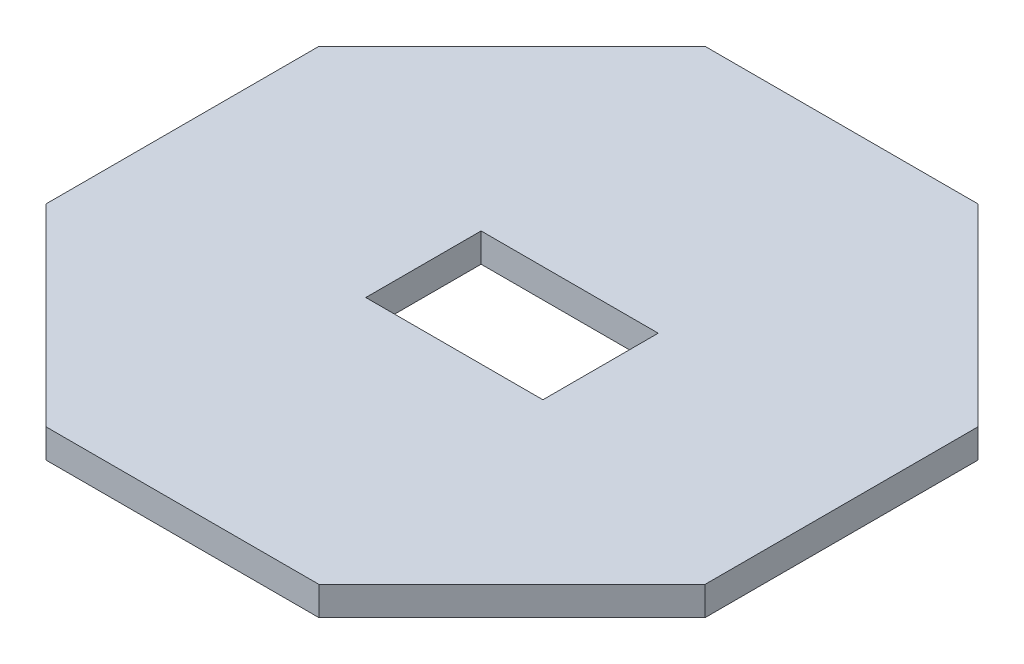
SolidWorks part; units mm, degrees
ref_plane "Front Plane" through (0, 0, 0) normal (0, 0, 1) x (1, 0, 0)
ref_plane "Top Plane" through (0, 0, 0) normal (0, 1, 0) x (1, 0, 0)
ref_plane "Right Plane" through (0, 0, 0) normal (1, 0, 0) x (0, 0, -1)
sketch "Sketch1" plane through (0, 0, 0) normal (0, 1, 0) x (1, 0, 0)
  line L1 (40, 16.5685) -> (16.5685, 40)
  line L2 (16.5685, 40) -> (-16.5685, 40)
  line L3 (-16.5685, 40) -> (-40, 16.5685)
  line L4 (-40, 16.5685) -> (-40, -16.5685)
  line L5 (-40, -16.5685) -> (-16.5685, -40)
  line L6 (-16.5685, -40) -> (16.5685, -40)
  line L7 (16.5685, -40) -> (40, -16.5685)
  line L8 (40, -16.5685) -> (40, 16.5685)
  line L9 (-10.75, -7) -> (10.75, -7)
  line L10 (-10.75, -7) -> (-10.75, 7)
  line L11 (-10.75, 7) -> (10.75, 7)
  line L12 (10.75, -7) -> (10.75, 7)
  line L13 (-10.75, -7) -> (10.75, 7) construction
  line L14 (-10.75, 7) -> (10.75, -7) construction
  circle A0 centre (0, 0) radius 40 construction
  point P1 (0, 40)
  dimension "D1" = 80
  dimension "D2" = 14
  dimension "D3" = 21.5
extrude "Boss-Extrude1" add sketch "Sketch1" along normal blind 3.5
